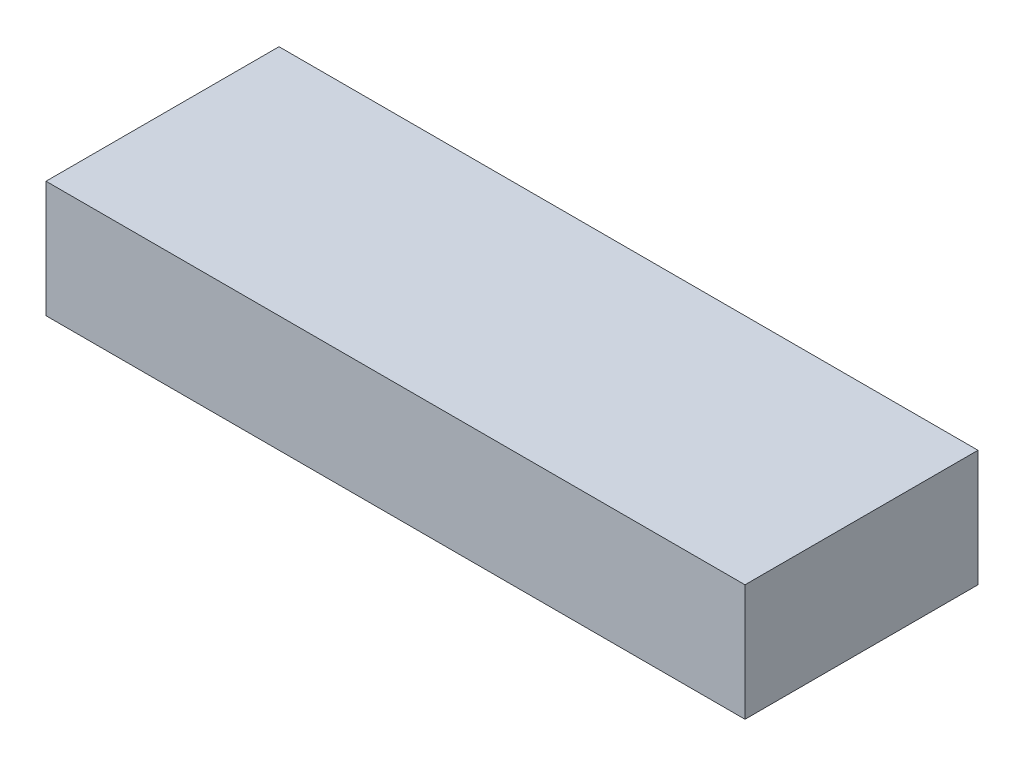
SolidWorks part; units mm, degrees
material "Plain Carbon Steel"
ref_plane "Front Plane" through (0, 0, 0) normal (0, 0, 1) x (1, 0, 0)
ref_plane "Top Plane" through (0, 0, 0) normal (0, 1, 0) x (1, 0, 0)
ref_plane "Right Plane" through (0, 0, 0) normal (1, 0, 0) x (0, 0, -1)
sketch "Sketch1" plane through (0, 0, 0) normal (0, 1, 0) x (1, 0, 0)
  line L1 (19.05, 6.35) -> (-19.05, 6.35)
  line L2 (19.05, 6.35) -> (19.05, -6.35)
  line L3 (19.05, -6.35) -> (-19.05, -6.35)
  line L4 (-19.05, 6.35) -> (-19.05, -6.35)
  line L5 (19.05, 6.35) -> (-19.05, -6.35) construction
  line L6 (19.05, -6.35) -> (-19.05, 6.35) construction
  point P0 (0, 0)
  dimension "D1" = 12.7
  dimension "D2" = 38.1
extrude "Boss-Extrude1" add sketch "Sketch1" along normal mid plane 6.35
